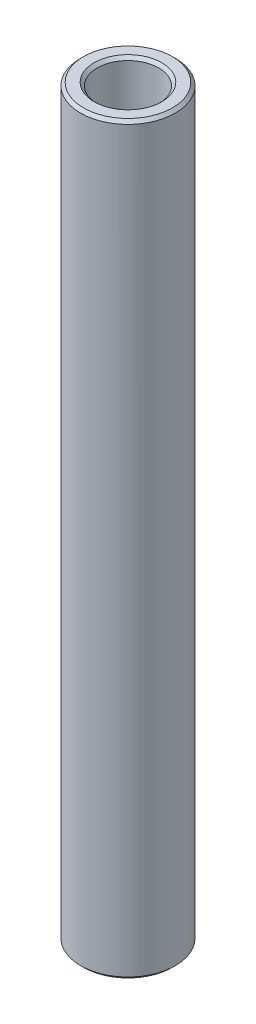
SolidWorks part; units mm, degrees
ref_plane "Front Plane" through (0, 0, 0) normal (0, 0, 1) x (1, 0, 0)
ref_plane "Top Plane" through (0, 0, 0) normal (0, 1, 0) x (1, 0, 0)
ref_plane "Right Plane" through (0, 0, 0) normal (1, 0, 0) x (0, 0, -1)
sketch "Sketch1" plane through (0, 0, 0) normal (0, 0, 1) x (1, 0, 0)
  line L0 (0, 9.6156) -> (0, -9.6156) construction
  line L1 (1.3, -15.6934) -> (2, -15.6934)
  line L2 (2, -15.6934) -> (2, 15.6934)
  line L3 (2, 15.6934) -> (1.3, 15.6934)
  line L4 (1.3, 15.6934) -> (1.3, -15.6934)
  point P7 (1.3, 0)
  dimension "D1" = 31.3868
  dimension "D2" = 4
  dimension "D3" = 2.6
revolve "Revolve1" add sketch "Sketch1" angle 360 about L0
chamfer "Chamfer1" distance 0.127 angle 45 4 edges at (0, -15.6934, 1.3) (0, -15.6934, 2) (0, 15.6934, 2) (0, 15.6934, 1.3)
